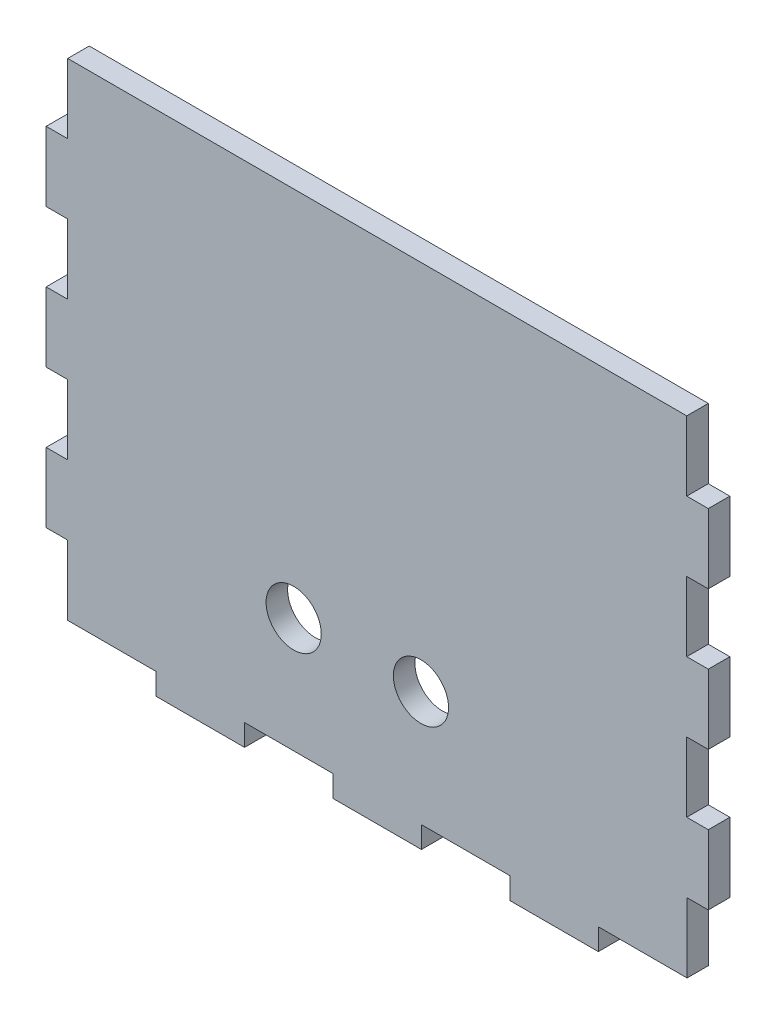
SolidWorks part; units mm, degrees
ref_plane "Front Plane" through (0, 0, 0) normal (0, 0, 1) x (1, 0, 0)
ref_plane "Top Plane" through (0, 0, 0) normal (0, 1, 0) x (1, 0, 0)
ref_plane "Right Plane" through (0, 0, 0) normal (1, 0, 0) x (0, 0, -1)
sketch "Sketch1" plane through (0, 0, 0) normal (0, 0, 1) x (1, 0, 0)
  line L0 (-37.709, -17.5649) -> (-25.4002, -17.5649)
  line L1 (-25.4002, -17.5649) -> (-25.4002, -20.5649)
  line L2 (-25.4002, -20.5649) -> (-13.0913, -20.5649)
  line L3 (-13.0913, -20.5649) -> (-13.0913, -17.5649)
  line L4 (-13.0913, -17.5649) -> (-0.7825, -17.5649)
  line L5 (-0.7825, -17.5649) -> (-0.7825, -20.5649)
  line L6 (-0.7825, -20.5649) -> (11.5264, -20.5649)
  line L7 (11.5264, -20.5649) -> (11.5264, -17.5649)
  line L8 (11.5264, -17.5649) -> (23.8352, -17.5649)
  line L9 (23.8352, -17.5649) -> (23.8352, -20.5649)
  line L10 (23.8352, -20.5649) -> (36.144, -20.5649)
  line L11 (36.144, -20.5649) -> (36.144, -17.5649)
  line L12 (36.144, -17.5649) -> (48.5002, -17.5649)
  line L13 (48.5002, -17.5649) -> (48.5002, -7.8881)
  line L14 (48.5002, -7.8881) -> (51.4529, -7.8881)
  line L15 (51.4529, -7.8881) -> (51.4529, 1.7888)
  line L16 (48.4529, 1.7888) -> (51.4529, 1.7888)
  line L17 (48.4529, 1.7888) -> (48.4529, 11.4657)
  line L18 (48.4529, 11.4657) -> (51.4529, 11.4657)
  line L19 (51.4529, 11.4657) -> (51.4529, 21.1425)
  line L20 (51.4529, 21.1425) -> (48.4529, 21.1425)
  line L21 (48.4529, 21.1425) -> (48.4529, 30.8194)
  line L22 (48.4529, 30.8194) -> (51.4529, 30.8194)
  line L23 (51.4529, 30.8194) -> (51.4529, 40.4963)
  line L24 (51.4529, 40.4963) -> (48.4529, 40.4963)
  line L25 (48.4529, 40.4963) -> (48.4529, 50.1731)
  line L26 (48.4529, 50.1731) -> (-37.709, 50.1731)
  line L27 (-37.709, 50.1731) -> (-37.709, 40.4963)
  line L28 (-37.709, 40.4963) -> (-40.709, 40.4963)
  line L29 (-40.709, 40.4963) -> (-40.709, 30.8194)
  line L30 (-40.709, 30.8194) -> (-37.709, 30.8194)
  line L31 (-37.709, 30.8194) -> (-37.709, 21.1425)
  line L32 (-37.709, 21.1425) -> (-40.709, 21.1425)
  line L33 (-40.709, 21.1425) -> (-40.709, 11.4657)
  line L34 (-40.709, 11.4657) -> (-37.709, 11.4657)
  line L35 (-37.709, 11.4657) -> (-37.709, 1.7888)
  line L36 (-37.709, 1.7888) -> (-40.709, 1.7888)
  line L37 (-40.709, 1.7888) -> (-40.709, -7.8881)
  line L38 (-40.709, -7.8881) -> (-37.709, -7.8881)
  line L39 (-37.709, -7.8881) -> (-37.709, -17.5649)
  dimension "D1" = 86.1619
  dimension "D2" = 67.738
  dimension "D3" = 9.6769
  dimension "D4" = 9.6769
  dimension "D5" = 9.6769
  dimension "D6" = 9.6769
  dimension "D7" = 9.6769
  dimension "D8" = 9.6769
  dimension "D9" = 12.3088
  dimension "D10" = 12.3088
  dimension "D11" = 12.3088
  dimension "D12" = 12.3088
  dimension "D13" = 12.3088
  dimension "D14" = 12.3088
  dimension "D15" = 3
  dimension "D16" = 3
  dimension "D17" = 3
extrude "Boss-Extrude1" add sketch "Sketch1" along normal blind 3
sketch "Sketch2" plane through (0, 0, 3) normal (0, 0, 1) x (1, 0, 0)
  circle A0 centre (-6.2581, -1.5681) radius 3.8411
  circle A1 centre (11.4568, -1.5681) radius 3.8411
  dimension "D1" = 7.6822
  dimension "D2" = 7.6822
extrude "Cut-Extrude1" cut sketch "Sketch2" against normal blind 3
equation "\"D3@Sketch1\"=\"D2@Sketch1\"/7"
equation "\"D4@Sketch1\"=\"D3@Sketch1\""
equation "\"D5@Sketch1\"=\"D3@Sketch1\""
equation "\"D6@Sketch1\"=\"D3@Sketch1\""
equation "\"D7@Sketch1\"=\"D3@Sketch1\""
equation "\"D8@Sketch1\"=\"D3@Sketch1\""
equation "\"D9@Sketch1\"=\"D1@Sketch1\"/7"
equation "\"D10@Sketch1\"=\"D9@Sketch1\""
equation "\"D11@Sketch1\"=\"D9@Sketch1\""
equation "\"D12@Sketch1\"=\"D9@Sketch1\""
equation "\"D13@Sketch1\"=\"D9@Sketch1\""
equation "\"D14@Sketch1\"=\"D9@Sketch1\""
equation "\"D16@Sketch1\"=\"D15@Sketch1\""
equation "\"D17@Sketch1\"=\"D15@Sketch1\""
equation "\"D2@Sketch2\"=\"D1@Sketch2\""
